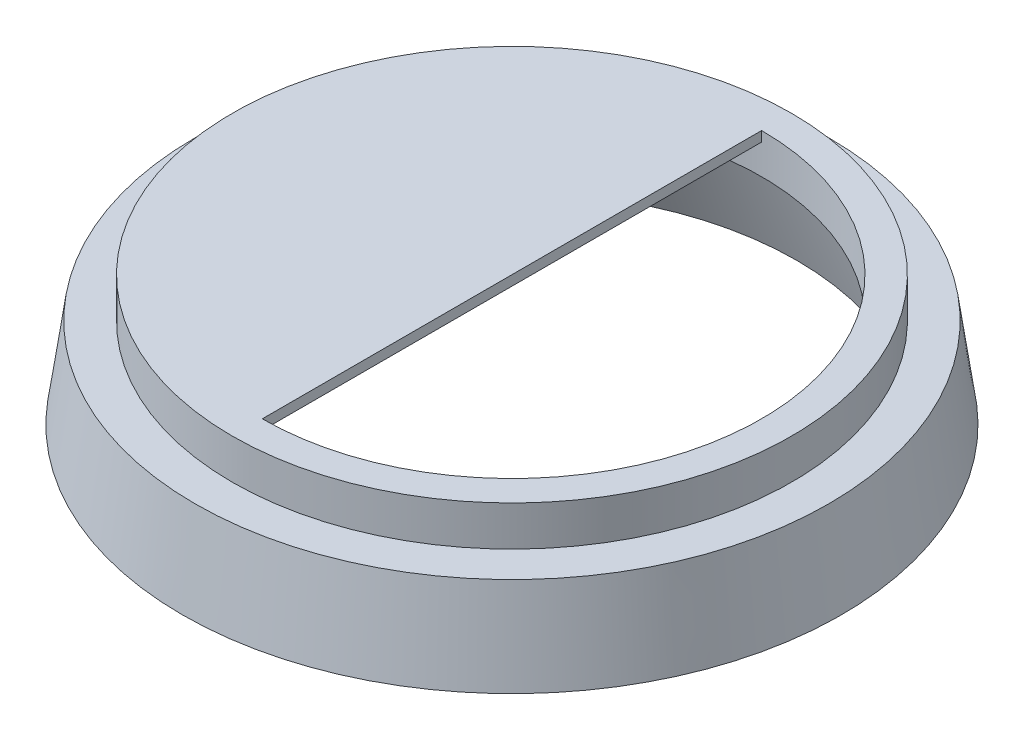
SolidWorks part; units mm, degrees
ref_plane "Front Plane" through (0, 0, 0) normal (0, 0, 1) x (1, 0, 0)
ref_plane "Top Plane" through (0, 0, 0) normal (0, 1, 0) x (1, 0, 0)
ref_plane "Right Plane" through (0, 0, 0) normal (1, 0, 0) x (0, 0, -1)
sketch "Sketch1" plane through (0, 0, 0) normal (0, 1, 0) x (1, 0, 0)
  circle A0 centre (0, 0) radius 16.5
  dimension "D1" = 33
extrude "Boss-Extrude1" add sketch "Sketch1" along normal blind 6.5 draft 8
sketch "Sketch2" plane through (0, 0, 0) normal (0, -1, 0) x (1, 0, 0)
  circle A0 centre (0, 0) radius 14.25
  dimension "D1" = 28.5
extrude "Cut-Extrude1" cut sketch "Sketch2" against normal blind 4.5 draft 21
sketch "Sketch3" plane through (0, 6.5, 0) normal (0, 1, 0) x (1, 0, 0)
  line L0 (0, -12.5) -> (0, 12.5)
  arc A0 (0, -12.5) -> (0, 12.5) centre (0, 0) ccw
  dimension "D1" = 25
extrude "Cut-Extrude2" cut sketch "Sketch3" against normal blind 6
chamfer "Chamfer1" distance 1.5 angle 45 1 edges at (0, 4.5, 0)
sketch "Sketch4" plane through (0, 6.5, 0) normal (0, 1, 0) x (1, 0, 0)
  circle A0 centre (0, 0) radius 14
  circle A1 centre (0, 0) radius 17.2951
extrude "Cut-Extrude3" cut sketch "Sketch4" against normal blind 2
